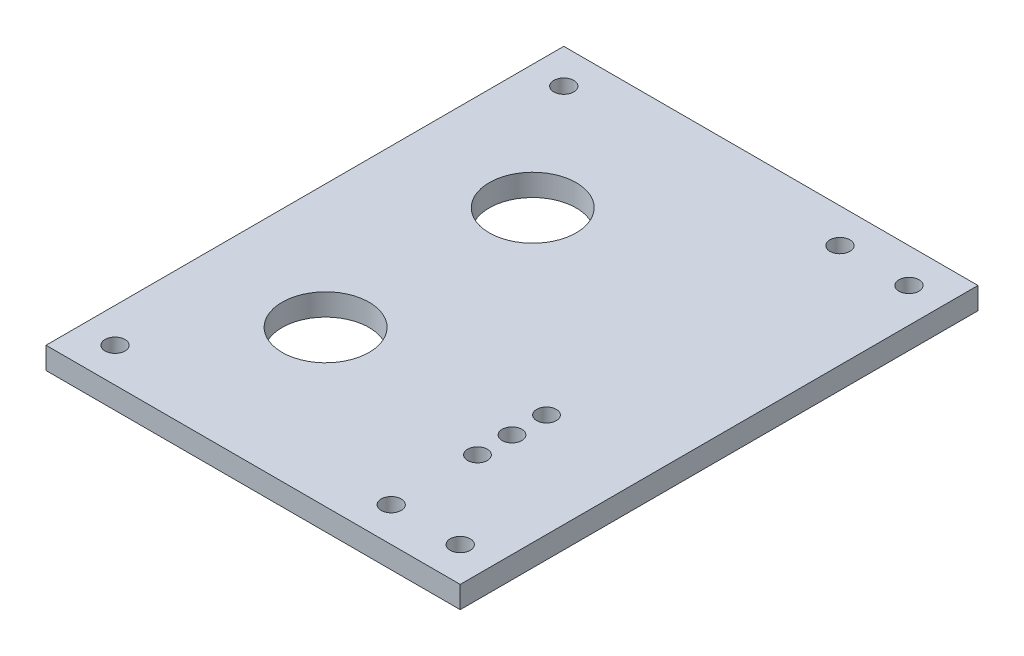
SolidWorks part; units mm, degrees
ref_plane "Front Plane" through (0, 0, 0) normal (0, 0, 1) x (1, 0, 0)
ref_plane "Top Plane" through (0, 0, 0) normal (0, 1, 0) x (1, 0, 0)
ref_plane "Right Plane" through (0, 0, 0) normal (1, 0, 0) x (0, 0, -1)
sketch "Sketch1" plane through (0, 0, 0) normal (0, 1, 0) x (1, 0, 0)
  line L1 (-30, -37.5) -> (30, -37.5)
  line L2 (-30, -37.5) -> (-30, 37.5)
  line L3 (-30, 37.5) -> (30, 37.5)
  line L4 (30, -37.5) -> (30, 37.5)
  line L5 (-30, -37.5) -> (30, 37.5) construction
  line L6 (-30, 37.5) -> (30, -37.5) construction
  point P0 (0, 0)
  dimension "D1" = 75
  dimension "D2" = 60
extrude "Boss-Extrude1" add sketch "Sketch1" along normal blind 3.175
sketch "Sketch2" plane through (0, 3.175, 0) normal (0, 1, 0) x (1, 0, 0)
  line L0 (30, -37.5) -> (30, 37.5) construction
  line L1 (25, 32.5) -> (-25, 32.5) construction
  line L2 (25, 32.5) -> (25, 0) construction
  line L3 (25, 0) -> (-25, 0) construction
  line L4 (-25, 32.5) -> (-25, 0) construction
  line L5 (30, 37.5) -> (-30, 37.5) construction
  circle A0 centre (25, 32.5) radius 1.45
  circle A1 centre (-25, 32.5) radius 1.45
  circle A2 centre (15, 32.5) radius 1.45
  circle A3 centre (25, -32.5) radius 1.45
  circle A4 centre (15, -32.5) radius 1.45
  circle A5 centre (-25, -32.5) radius 1.45
  dimension "D3" = 2.9
  dimension "D1" = 5
  dimension "D2" = 5
  dimension "D4" = 10
extrude "Cut-Extrude1" cut sketch "Sketch2" against normal through all
sketch "Sketch3" plane through (0, 3.175, 0) normal (0, 1, 0) x (-1, 0, 0)
  line L0 (-15, 20) -> (-15, 15) construction
  circle A0 centre (12, -15) radius 6.3
  circle A1 centre (12, 15) radius 6.3
  circle A2 centre (-15, 20) radius 1.425
  circle A3 centre (-15, 15) radius 1.425
  circle A4 centre (-15, 10) radius 1.425
  dimension "D1" = 12.6
  dimension "D5" = 2.85
  dimension "D2" = 30
  dimension "D3" = 15
  dimension "D4" = 12
  dimension "D6" = 15
  dimension "D7" = 20
  dimension "D9" = 5
  dimension "D8" = 3
extrude "Cut-Extrude2" cut sketch "Sketch3" against normal through all
